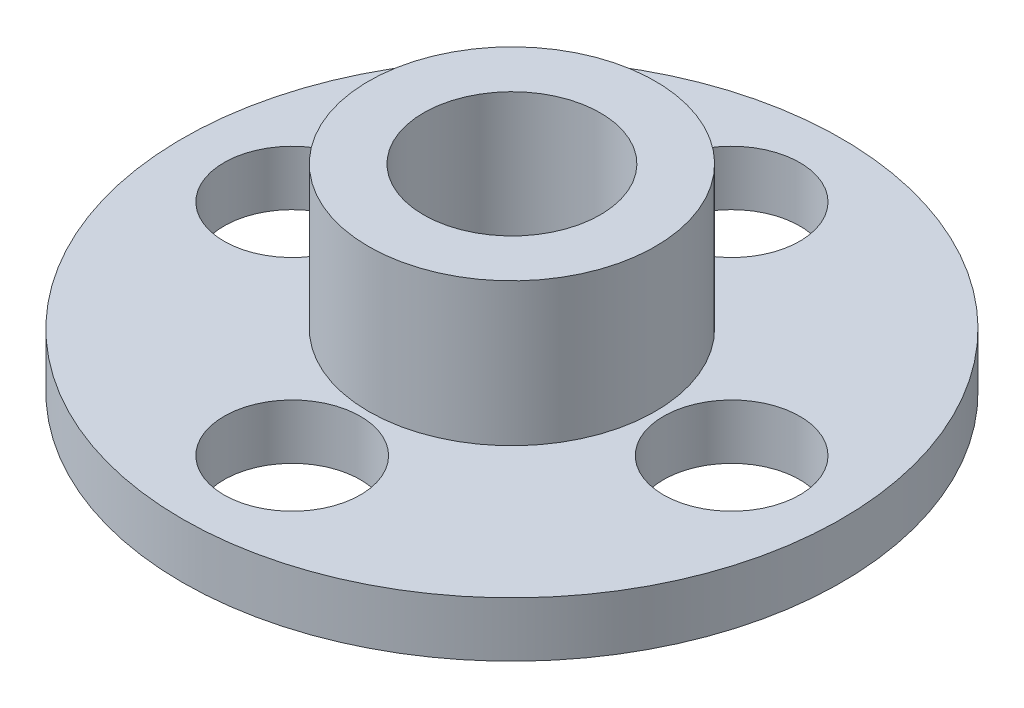
SolidWorks part; units mm, degrees
ref_plane "Front Plane" through (0, 0, 0) normal (0, 0, 1) x (1, 0, 0)
ref_plane "Top Plane" through (0, 0, 0) normal (0, 1, 0) x (1, 0, 0)
ref_plane "Right Plane" through (0, 0, 0) normal (1, 0, 0) x (0, 0, -1)
sketch "Sketch1" plane through (0, 0, 0) normal (0, 1, 0) x (1, 0, 0)
  circle A0 centre (0, 0) radius 19.05
  circle A1 centre (0, 0) radius 5.08
  circle A2 centre (0, 12.7) radius 3.9402
  circle A3 centre (12.7, 0) radius 3.9402
  circle A4 centre (0, -12.7) radius 3.9402
  circle A5 centre (-12.7, 0) radius 3.9402
  point P15 (0, 0)
  dimension "D1" = 38.1
  dimension "D4" = 10.16
  dimension "D2" = 12.7
  dimension "D3" = 4
extrude "Boss-Extrude1" add sketch "Sketch1" along normal blind 3.175
sketch "Sketch2" plane through (0, 3.175, 0) normal (0, 1, 0) x (1, 0, 0)
  circle A0 centre (0, 0) radius 5.1093
  circle A1 centre (0, 0) radius 8.2843
  dimension "D1" = 3.175
extrude "Boss-Extrude2" add sketch "Sketch2" along normal blind 8.255
